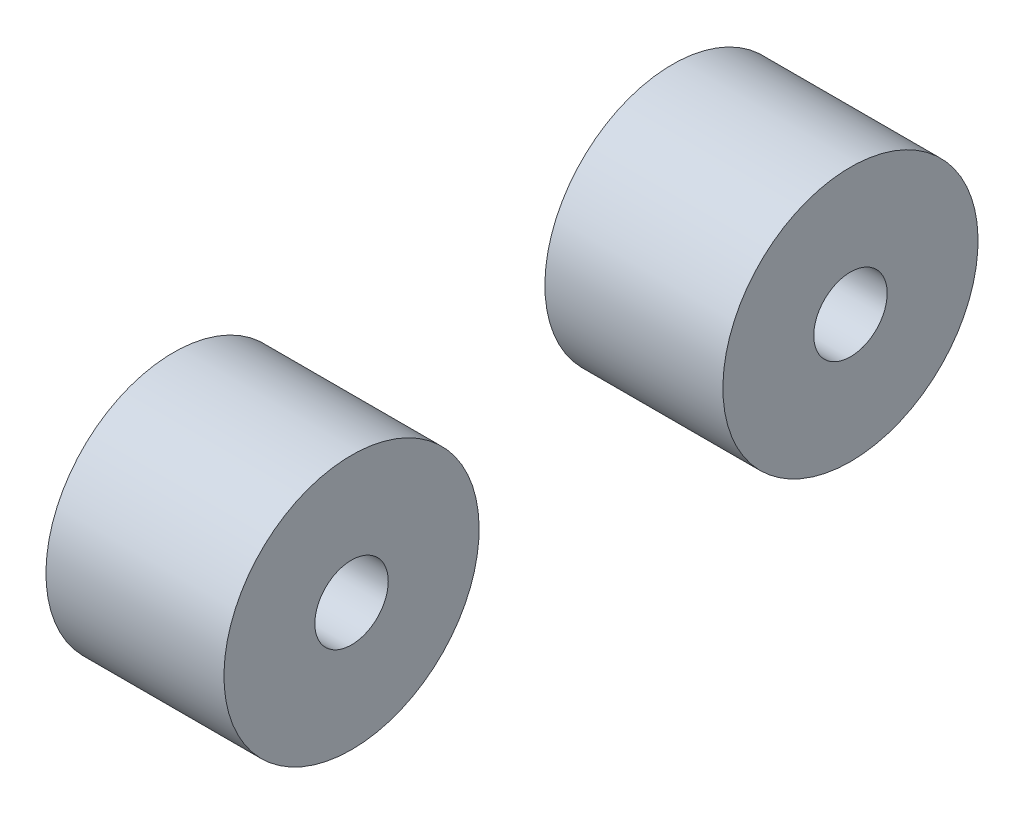
SolidWorks part; units mm, degrees
ref_plane "Front Plane" through (0, 0, 0) normal (0, 0, 1) x (1, 0, 0)
ref_plane "Top Plane" through (0, 0, 0) normal (0, 1, 0) x (1, 0, 0)
ref_plane "Right Plane" through (0, 0, 0) normal (1, 0, 0) x (0, 0, -1)
sketch "Sketch1" plane through (0, 0, 0) normal (0, 0, 1) x (1, 0, 0)
  line L0 (8.255, 0) -> (-8.255, 0) construction
  line L1 (26.255, 0) -> (-26.255, 0) construction
  line L2 (8.255, 0) -> (8.255, 12.9)
  line L3 (8.255, 12.9) -> (26.255, 12.9)
  line L4 (26.255, 12.9) -> (26.255, 0)
  line L5 (8.255, 0) -> (26.255, 0)
  point P4 (0, 0)
  point P8 (0, 0)
  dimension "D1" = 18
  dimension "D2" = 16.51
  dimension "D3" = 12.9
revolve "Revolve1" add sketch "Sketch1" angle 360 about L5
sketch "Sketch2" plane through (8.255, 0, 0) normal (-1, 0, 0) x (0, 0, 1)
  circle A0 centre (0, 0) radius 3.7138
  dimension "D1" = 7.4275
extrude "Cut-Extrude1" cut sketch "Sketch2" against normal blind 7.5725
sketch "Sketch3" plane through (26.255, 0, 0) normal (1, 0, 0) x (0, 0, -1)
  line L0 (-20.8953, -55) -> (-20.8953, -46.1532)
  line L1 (13.175, -55) -> (-13.175, -55) construction
  line L2 (13.175, -55) -> (13.175, 55) construction
  line L3 (13.175, 55) -> (-13.175, 55) construction
  line L4 (-13.175, -55) -> (-13.175, 55) construction
  line L5 (13.175, -55) -> (-13.175, 55) construction
  line L6 (13.175, 55) -> (-13.175, -55) construction
  line L7 (-24.3823, -32.1152) -> (-32.3245, -17.1152)
  line L9 (-5.4548, -55) -> (-5.4548, -44)
  line L11 (5.4547, -44) -> (5.4547, -55)
  line L12 (20.8953, -55) -> (20.8953, -46.1532)
  line L13 (24.3823, -32.1152) -> (32.3245, -17.1152)
  line L14 (55, 0) -> (-55, 0) construction
  line L15 (13.175, -55) -> (-13.175, 55) construction
  line L16 (13.175, 55) -> (-13.175, -55) construction
  line L17 (13.175, 55) -> (-13.175, 55) construction
  line L18 (24.3823, 32.1152) -> (32.3245, 17.1152)
  line L19 (20.8953, 55) -> (20.8953, 46.1532)
  line L20 (5.4547, 44) -> (5.4547, 55)
  line L21 (-5.4548, 55) -> (-5.4548, 44)
  line L22 (-24.3823, 32.1152) -> (-32.3245, 17.1152)
  line L23 (-20.8953, 55) -> (-20.8953, 46.1532)
  arc A15 (32.3245, -17.1152) -> (32.3245, 17.1152) centre (0, 0) ccw
  arc A16 (-5.4548, 55) -> (-20.8953, 55) centre (-13.175, 55) ccw
  arc A17 (-20.8953, -55) -> (-5.4548, -55) centre (-13.175, -55) ccw
  arc A18 (5.4547, -55) -> (20.8953, -55) centre (13.175, -55) ccw
  arc A19 (20.8953, 55) -> (5.4547, 55) centre (13.175, 55) ccw
  arc A20 (-5.4548, -44) -> (5.4547, -44) centre (0, -44) cw
  arc A21 (20.8953, -46.1532) -> (24.3823, -32.1152) centre (50.8953, -46.1532) cw
  arc A22 (-20.8953, -46.1532) -> (-24.3823, -32.1152) centre (-50.8953, -46.1532) ccw
  arc A23 (-20.8953, 46.1532) -> (-24.3823, 32.1152) centre (-50.8953, 46.1532) cw
  arc A24 (20.8953, 46.1532) -> (24.3823, 32.1152) centre (50.8953, 46.1532) ccw
  arc A25 (-5.4548, 44) -> (5.4547, 44) centre (0, 44) ccw
  arc A26 (5.4547, 55) -> (20.8953, 55) centre (13.175, 55) cw
  arc A27 (-20.8953, 55) -> (-5.4548, 55) centre (-13.175, 55) cw
  arc A29 (-32.3245, 17.1152) -> (-32.3245, -17.1152) centre (0, 0) ccw
  dimension "D3" = 15.4405
  dimension "D5" = 7.7203
  dimension "D4" = 30
  dimension "D7" = 15
  dimension "D9" = 110
  dimension "D1" = 73.152
  dimension "D6" = 15
  dimension "D2" = 26.35
  dimension "D8" = 11
sketch "Sketch4" plane through (26.255, 0, 0) normal (1, 0, 0) x (0, 0, -1)
  circle A0 centre (0, 0) radius 3.7138
  dimension "D1" = 7.4275
extrude "Cut-Extrude2" cut sketch "Sketch4" against normal blind 7.0725
move or copy body "Body-Move/Copy1" bodies to move or copy 114 copy yes number of copies 1 translate (0, 0, 50.4528)
